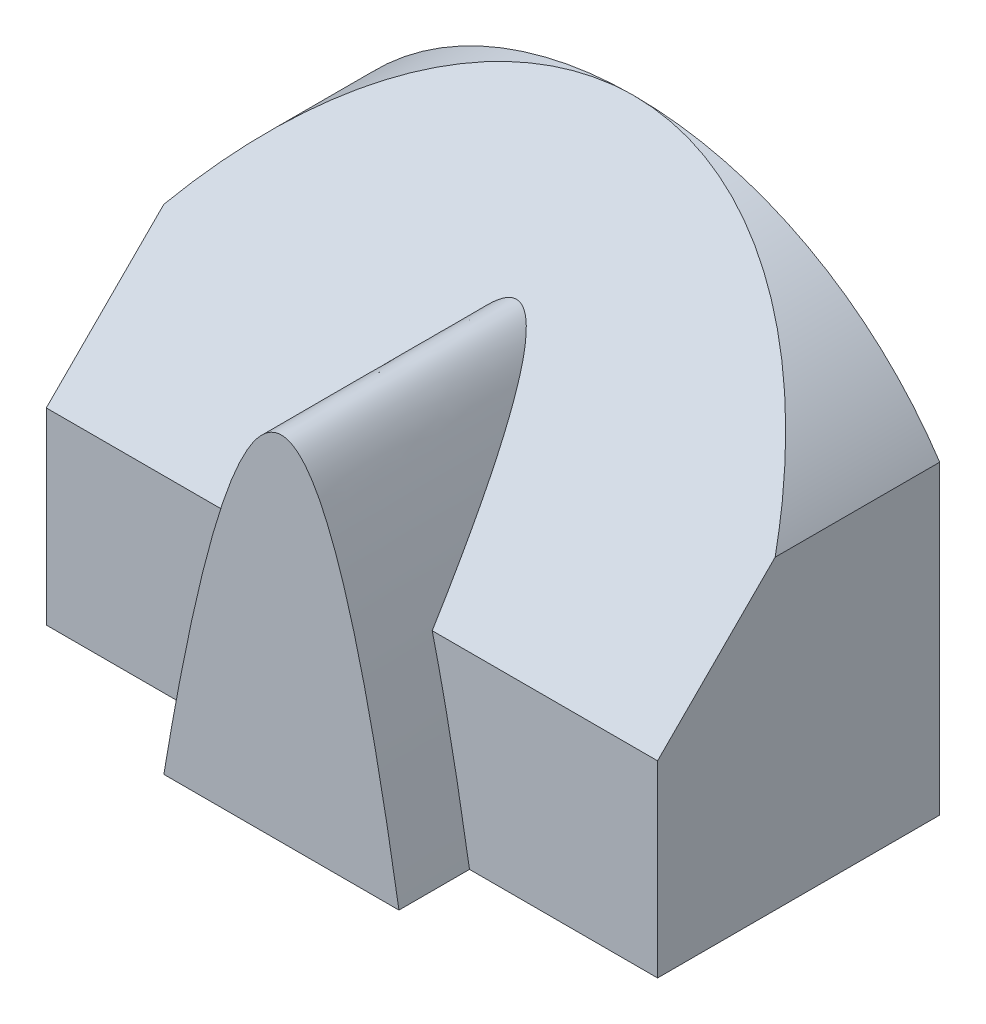
SolidWorks part; units mm, degrees
ref_plane "Front" through (0, 0, 0) normal (0, 0, 1) x (1, 0, 0)
ref_plane "Top" through (0, 0, 0) normal (0, 1, 0) x (1, 0, 0)
ref_plane "Right" through (0, 0, 0) normal (1, 0, 0) x (0, 0, -1)
sketch "Sketch1" plane through (0, 0, 0) normal (0, 0, 1) x (1, 0, 0)
  line L1 (0, 0) -> (130, 0)
  line L2 (0, 0) -> (0, 100)
  line L3 (0, 100) -> (130, 100)
  line L4 (130, 0) -> (130, 100)
  dimension "D1" = 130
  dimension "D2" = 100
extrude "Extrude1" add sketch "Sketch1" against normal blind 60
sketch "Sketch2" plane through (0, 0, 0) normal (0, 0, 1) x (1, 0, 0)
  line L1 (0, 100) -> (0, 0) construction
  line L2 (130, 0) -> (130, 100) construction
  line L3 (130, 100) -> (0, 100) construction
  line L4 (65, 100) -> (65, 6.4345) construction
  line L5 (0, 65) -> (0, 111.4996)
  line L6 (0, 111.4996) -> (130, 111.4996)
  line L7 (130, 111.4996) -> (130, 65)
  arc A0 (130, 65) -> (0, 65) centre (65, 22.1429) ccw
extrude "Cut-Extrude1" cut sketch "Sketch2" against normal through all
sketch "Sketch3" plane through (130, 0, 0) normal (1, 0, 0) x (0, 0, -1)
  line L0 (60, 0) -> (0, 0) construction
  line L1 (0, 0) -> (0, 65) construction
  line L4 (0, 40) -> (60, 100)
  line L5 (60, 100) -> (0, 100)
  line L6 (0, 100) -> (0, 40)
  dimension "D1" = 40
extrude "Cut-Extrude2" cut sketch "Sketch3" against normal through all
sketch "Sketch4" plane through (0, 0, 0) normal (0, 0, 1) x (1, 0, 0)
  line L0 (65, 0) -> (65, 75) construction
  line L1 (0, 0) -> (130, 0) construction
  line L2 (90, 0) -> (90, 75) construction
  line L3 (40, 0) -> (40, 75) construction
  line L4 (40, 75) -> (90, 75) construction
  line L5 (90, 0) -> (90, 100) construction
  line L6 (40, 0) -> (40, 100) construction
  line L7 (65, 0) -> (65, 100) construction
  line L8 (40, 0) -> (90, 0)
  parabola Q0 (40, 0) -> (90, 0) focus (65, 72.9167) apex (65, 75)
  dimension "D1" = 75
  dimension "D3" = 25
extrude "Extrude2" add sketch "Sketch4" along normal blind 15 and the other way blind 55
